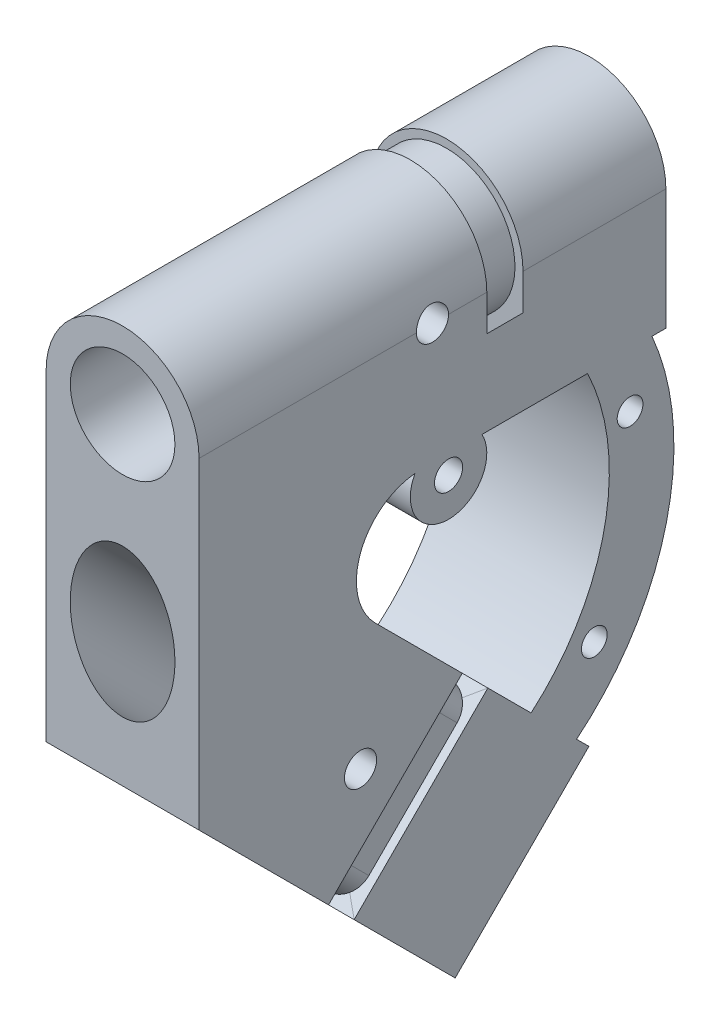
SolidWorks part; units mm, degrees
ref_plane "Alzado" through (0, 0, 0) normal (0, 0, 1) x (1, 0, 0)
ref_plane "Planta" through (0, 0, 0) normal (0, 1, 0) x (1, 0, 0)
ref_plane "Vista lateral" through (0, 0, 0) normal (1, 0, 0) x (0, 0, -1)
sketch "Croquis1" plane through (0, 0, 0) normal (0, 0, 1) x (1, 0, 0)
  line L0 (0, 0) -> (0, -15) construction
  line L1 (-9.5, -15) -> (9.5, -15)
  line L2 (-9.5, -15) -> (-9.5, 0)
  line L3 (9.5, -15) -> (9.5, 0)
  circle A0 centre (0, 0) radius 6.5
  arc A1 (9.5, 0) -> (-9.5, 0) centre (0, 0) ccw
  point P8 (0, -15)
  dimension "D1" = 13
  dimension "D2" = 3
  dimension "D3" = 15
extrude "Saliente-Extruir1" add sketch "Croquis1" against normal mid plane 58
ref_plane "Plano1" through (0, -15, 0) normal (0, -1, 0) x (-1, 0, 0)
sketch "Croquis2" plane through (0, 0, 0) normal (1, 0, 0) x (0, 0, -1)
  line L0 (-29, -15) -> (-29, -40)
  line L1 (-29, -40) -> (2.8198, -71.8198)
  line L4 (29, -15) -> (-29, -15) construction
  line L5 (2.8198, -71.8198) -> (19.4368, -55.2028)
  line L6 (11.1283, -63.5113) -> (-29, -23.383) construction
  line L7 (-29, -15) -> (-1.4523, -15)
  line L8 (-7.1091, -28.6569) -> (19.4368, -55.2028)
  arc A0 (-7.1091, -28.6569) -> (-1.4523, -15) centre (-1.4523, -23) cw
  dimension "D3" = 8
  dimension "D1" = 135
  dimension "D2" = 23.5
  dimension "D4" = 45
  dimension "D5" = 25
extrude "Saliente-Extruir2" add sketch "Croquis2" along direction (1, 0, 0) on the side of the normal up to surface (9.5 mm away) and the other way up to surface (9.5 mm away)
ref_plane "Plano3" through (0, -37.3198, -37.3198) normal (0, -0.7071, -0.7071) x (-1, 0, 0)
sketch "Croquis4" plane through (0, -37.3198, -37.3198) normal (0, -0.7071, -0.7071) x (-1, 0, 0)
  line L0 (0, -25.2904) -> (0, -48.7904) construction
  line L1 (-9.5, -25.2904) -> (9.5, -25.2904) construction
  line L2 (-9.5, -48.7904) -> (9.5, -48.7904) construction
  circle A0 centre (0, -37.0404) radius 6.5
  dimension "D1" = 13
extrude "Cortar-Extruir1" cut sketch "Croquis4" against normal blind 80
sketch "Croquis7" plane through (0, 0, 0) normal (1, 0, 0) x (0, 0, -1)
  line L0 (19.4368, -55.2028) -> (-7.1091, -28.6569) construction
  line L1 (29, -15) -> (29, 0) construction
  line L2 (2.8198, -71.8198) -> (19.4368, -55.2028) construction
  line L3 (29, -15) -> (-1.4523, -15) construction
  line L4 (19.2702, -15) -> (27.2702, -15)
  line L5 (12.2509, -48.0169) -> (17.9078, -53.6738)
  arc A0 (12.2509, -48.0169) -> (19.2702, -15) centre (-5.7469, -26.9361) ccw
  arc A1 (27.2702, -15) -> (17.9078, -53.6738) centre (-3, -28.1421) cw
  dimension "D1" = 8
  dimension "D3" = 3
  dimension "D4" = 32
  dimension "D5" = 35
  dimension "D6" = 33
  dimension "D2" = 8
extrude "Saliente-Extruir3" add sketch "Croquis7" along normal up to surface and the other way up to surface
sketch "Croquis8" plane through (0, 0, 0) normal (1, 0, 0) x (0, 0, -1)
  line L0 (-29, 0) -> (-29, -40) construction
  circle A0 centre (2, -17.3114) radius 1.75
  circle A1 centre (2, -17.3114) radius 4.75
  dimension "D1" = 3
  dimension "D2" = 3.5
  dimension "D3" = 31
extrude "Saliente-Extruir4" add sketch "Croquis8" against normal up to surface and the other way up to surface
sketch "Croquis9" plane through (0, 0, 0) normal (1, 0, 0) x (0, 0, -1)
  circle A0 centre (24.5509, -21.7313) radius 1.6
  circle A1 centre (20.1094, -44.2984) radius 1.6
  circle A2 centre (2, -17.3114) radius 1.75 construction
  dimension "D1" = 3.2
  dimension "D2" = 22.98
  dimension "D3" = 32.5
  dimension "D4" = 23
extrude "Cortar-Extruir2" cut sketch "Croquis9" against normal mid plane 21
sketch "Croquis10" plane through (0, 0, 0) normal (1, 0, 0) x (0, 0, -1)
  line L0 (29, 0) -> (-29, 0) construction
  line L1 (11.1283, -63.5113) -> (-29, -23.383) construction
  line L2 (2.8198, -71.8198) -> (19.4368, -55.2028) construction
  line L3 (-29, 0) -> (-29, -40) construction
  circle A0 centre (0, 0) radius 2
  circle A1 centre (-8.9358, -43.4471) radius 2
  dimension "D1" = 4
extrude "Cortar-Extruir3" cut sketch "Croquis10" along normal mid plane 40
ref_plane "Plano4" through (0, -23.1777, -23.1777) normal (0, -0.7071, -0.7071) x (-1, 0, 0)
sketch "Croquis11" plane through (0, -23.1777, -23.1777) normal (0, -0.7071, -0.7071) x (-1, 0, 0)
  line L0 (-9.5, -48.7904) -> (-9.5, -25.2904) construction
  line L1 (-9.5, -48.7904) -> (9.5, -48.7904) construction
  line L2 (9.5, -48.7904) -> (9.5, -25.2904) construction
  line L3 (-9.5, -25.2904) -> (9.5, -25.2904) construction
  line L4 (-9.5, -48.7904) -> (-9.5, -25.2904)
  line L5 (-9.5, -48.7904) -> (9.5, -48.7904)
  line L6 (9.5, -48.7904) -> (9.5, -25.2904)
  line L7 (-9.5, -25.2904) -> (9.5, -25.2904)
sketch "Croquis12" plane through (-9.5, 0, 0) normal (-1, 0, 0) x (0, 0, 1)
  line L0 (-3.7037, -39.4697) -> (-6.8857, -42.6517)
  line L1 (-12.2509, -48.0169) -> (7.1091, -28.6569) construction
  line L2 (-6.8857, -42.6517) -> (-6.1786, -43.3588)
  line L3 (-6.1786, -43.3588) -> (-2.9966, -40.1768)
  line L4 (-2.9966, -40.1768) -> (-3.7037, -39.4697)
  line L5 (-5.2947, -41.0607) -> (11.3223, -57.6777) construction
  line L6 (29, -40) -> (-2.8198, -71.8198) construction
  line L7 (-2.8198, -71.8198) -> (-19.4368, -55.2028) construction
  dimension "D1" = 20
  dimension "D2" = 4.5
  dimension "D3" = 1
sweep "Cortar-Barrer1" cut profiles "Croquis12" path "Croquis11"
fillet "Redondeo1" radius 3 4 edges at (-8.5, -56.9706, 10.6152) (8.5, -41.7678, -4.5876) (-8.5, -41.7678, -4.5876) (8.5, -56.9706, 10.6152)
ref_plane "Plano5" through (0, 0, -9) normal (0, 0, -1) x (-1, 0, 0)
sketch "Croquis13" plane through (0, 0, 0) normal (1, 0, 0) x (0, 0, -1)
  line L0 (29, 9.5) -> (-29, 9.5) construction
  line L2 (6.75, 10.5) -> (6.75, 8.5)
  line L3 (6.75, 8.5) -> (11.25, 8.5)
  line L4 (11.25, 10.5) -> (11.25, 8.5)
  line L5 (29, 9.5) -> (-29, 9.5) construction
  line L6 (9, 9.5) -> (9, -15) construction
  line L7 (19.2702, -15) -> (6.1497, -15) construction
  line L8 (29, 0) -> (29, 9.5) construction
  line L9 (6.75, 10.5) -> (11.25, 10.5)
  point P12 (6.75, 9.5)
  dimension "D1" = 4.5
  dimension "D2" = 2
  dimension "D3" = 20
  dimension "D4" = 9.5
sketch "Croquis14" plane through (0, 0, -9) normal (0, 0, -1) x (-1, 0, 0)
  circle A0 centre (0, 0) radius 6.5 construction
  circle A1 centre (0, 0) radius 6.5 construction
  circle A2 centre (0, 0) radius 9.5
  dimension "D1" = 19
sweep "Cortar-Barrer3" cut profiles "Croquis13" path "Croquis14"
